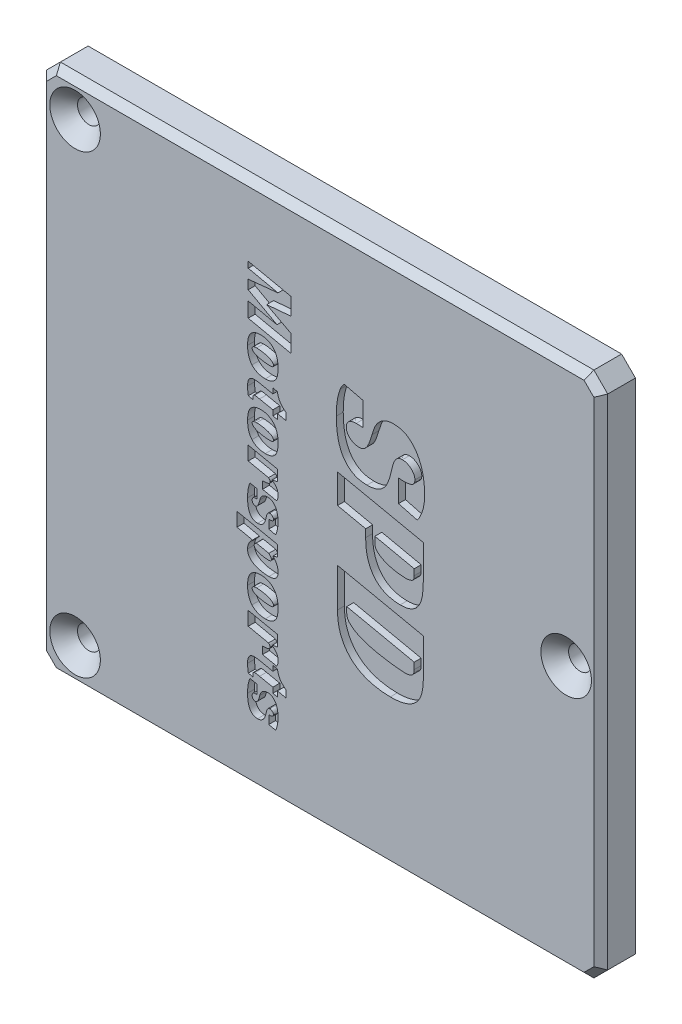
SolidWorks part; units mm, degrees
ref_plane "Front Plane" through (0, 0, 0) normal (0, 0, 1) x (1, 0, 0)
ref_plane "Top Plane" through (0, 0, 0) normal (0, 1, 0) x (1, 0, 0)
ref_plane "Right Plane" through (0, 0, 0) normal (1, 0, 0) x (0, 0, -1)
sketch "Sketch1" plane through (0, 0, 0) normal (0, 0, 1) x (1, 0, 0)
  line L0 (-40, 35) -> (-41, 35) construction
  line L1 (-2, -29) -> (-28, -29) construction
  line L2 (-2, -29) -> (-2, 29) construction
  line L3 (-2, 29) -> (-28, 29) construction
  line L4 (-28, -29) -> (-28, 29) construction
  line L5 (-2, -29) -> (-28, 29) construction
  line L6 (-2, 29) -> (-28, -29) construction
  line L7 (35, -35) -> (-40, -35)
  line L8 (35, -35) -> (35, 35)
  line L9 (35, 35) -> (-40, 35)
  line L10 (-40, -35) -> (-40, 35)
  line L11 (35, -35) -> (-40, 35) construction
  line L12 (35, 35) -> (-40, -35) construction
  line L13 (-40, 35) -> (-40, 36) construction
  line L14 (-41, 35) -> (-5, 35) construction
  line L15 (36, -36) -> (-41, -36)
  line L16 (36, -36) -> (36, 36)
  line L17 (36, 36) -> (-41, 36)
  line L18 (-41, -36) -> (-41, 36)
  line L19 (36, -36) -> (-41, 36) construction
  line L20 (36, 36) -> (-41, -36) construction
  line L21 (-40, 36) -> (-40, 38) construction
  line L22 (0, 0) -> (-15, 0)
  line L23 (38, -38) -> (-43, -38)
  line L24 (38, -38) -> (38, 38)
  line L25 (38, 38) -> (-43, 38)
  line L26 (-43, -38) -> (-43, 38)
  line L27 (38, -38) -> (-43, 38) construction
  line L28 (38, 38) -> (-43, -38) construction
  circle A0 centre (-2, 29) radius 1.25
  circle A1 centre (-28, 29) radius 1.25
  circle A2 centre (-2, -29) radius 1.25
  circle A3 centre (-28, -29) radius 1.25
  point P0 (-15, 0)
  point P10 (-15, 0)
  point P15 (-15, 0)
  point P18 (-15, 0)
  point P24 (-15, 0)
  dimension "D3" = 1
  dimension "D1" = 58
  dimension "D2" = 26
  dimension "D4" = 1
  dimension "D5" = 75
  dimension "D6" = 70
  dimension "D7" = 72
  dimension "D8" = 76
  dimension "D9" = 15
extrude "Boss-Extrude1" add sketch "Sketch1" along normal blind 5
chamfer "Chamfer3" distance 2 angle 45 4 edges at (-43, 38, 2.5) (-43, -38, 2.5) (38, -38, 2.5) (38, 38, 2.5)
sketch "Sketch3" plane through (0, 0, 0) normal (0, 0, -1) x (-1, 0, 0)
  line L0 (-34.92, 32.1764) -> (-34.92, 3.9876)
  line L1 (-33.5482, 34.3518) -> (-34.3518, 33.5482)
  line L2 (-34.92, 1.93) -> (-36, 1.75)
  line L3 (39.77, -26.8512) -> (39.77, 26.8512)
  line L4 (31.7012, 34.92) -> (-32.1764, 34.92)
  line L5 (-34.92, 3.9876) -> (-34.92, 1.93)
  line L6 (-34.3518, -33.5482) -> (-33.5482, -34.3518)
  line L7 (-36, 4.1109) -> (-36, 1.75)
  line L8 (-32.1764, -34.92) -> (31.7012, -34.92)
  line L9 (-34.92, -3.9876) -> (-34.92, -32.1764)
  line L10 (0, 0) -> (-7.0484, 0) construction
  line L11 (-36, -4.1109) -> (-36, -1.75)
  line L12 (-34.92, -3.9876) -> (-34.92, -1.93)
  line L13 (-34.92, -1.93) -> (-36, -1.75)
  line L20 (-34, -36) -> (36.7574, -36)
  line L21 (41, -31.7574) -> (41, 31.7574)
  line L22 (36.7574, 36) -> (-34, 36)
  line L23 (-34, 36) -> (-36, 34)
  line L24 (-36, 34) -> (-36, 1.75)
  line L25 (-36, 1.75) -> (-30, 2.75)
  line L26 (-30, 2.75) -> (-30, -2.75)
  line L27 (-30, -2.75) -> (-36, -1.75)
  line L28 (-36, -1.75) -> (-36, -34)
  line L29 (-36, -34) -> (-34, -36)
  line L30 (-33.1716, -36) -> (32.6816, -36)
  line L31 (41, -27.6816) -> (41, 27.6816)
  line L32 (32.6816, 36) -> (-33.1716, 36)
  line L33 (-34.5858, 35.4142) -> (-35.4142, 34.5858)
  line L34 (-36, 33.1716) -> (-36, 4.1109)
  line L38 (-36, -4.1109) -> (-36, -33.1716)
  line L39 (-35.4142, -34.5858) -> (-34.5858, -35.4142)
  arc A0 (-32.1764, -34.92) -> (-33.5482, -34.3518) centre (-32.1764, -32.98) cw
  arc A1 (33.5976, 32.5708) -> (37.4208, 28.7476) centre (36.7423, 31.8923) ccw
  arc A2 (37.4208, -28.7476) -> (33.5976, -32.5708) centre (36.7423, -31.8923) ccw
  arc A4 (-32.1764, 34.92) -> (-33.5482, 34.3518) centre (-32.1764, 32.98) ccw
  arc A13 (41, -31.7574) -> (36.7574, -36) centre (37.8787, -32.8787) ccw
  arc A14 (36.7574, 36) -> (41, 31.7574) centre (37.8787, 32.8787) ccw
  arc A15 (38.5782, -29.6367) -> (34.6367, -33.5782) centre (37.8787, -32.8787) ccw
  arc A16 (34.6367, 33.5782) -> (38.5782, 29.6367) centre (37.8787, 32.8787) ccw
  arc A17 (32.6816, -36) -> (34.6367, -33.5782) centre (32.6816, -34) ccw
  arc A18 (38.5782, -29.6367) -> (41, -27.6816) centre (39, -27.6816) ccw
  arc A19 (41, 27.6816) -> (38.5782, 29.6367) centre (39, 27.6816) ccw
  arc A20 (34.6367, 33.5782) -> (32.6816, 36) centre (32.6816, 34) ccw
  arc A21 (-36, -33.1716) -> (-35.4142, -34.5858) centre (-34, -33.1716) ccw
  arc A22 (-33.1716, -36) -> (-34.5858, -35.4142) centre (-33.1716, -34) cw
  arc A23 (-33.1716, 36) -> (-34.5858, 35.4142) centre (-33.1716, 34) ccw
  arc A24 (-35.4142, 34.5858) -> (-36, 33.1716) centre (-34, 33.1716) ccw
  arc A25 (39.77, 26.8512) -> (37.4208, 28.7476) centre (37.83, 26.8512) ccw
  arc A26 (-34.92, -32.1764) -> (-34.3518, -33.5482) centre (-32.98, -32.1764) ccw
  arc A28 (-34.3518, 33.5482) -> (-34.92, 32.1764) centre (-32.98, 32.1764) ccw
  arc A30 (33.5976, 32.5708) -> (31.7012, 34.92) centre (31.7012, 32.98) ccw
  arc A31 (37.4208, -28.7476) -> (39.77, -26.8512) centre (37.83, -26.8512) ccw
  arc A33 (31.7012, -34.92) -> (33.5976, -32.5708) centre (31.7012, -32.98) ccw
  dimension "D6" = 2
  dimension "D4" = 0
extrude "Boss-Extrude3" add sketch "Sketch3" along normal blind 2
sketch "Sketch4" plane through (0, 0, 0) normal (0, 0, -1) x (-1, 0, 0)
  line L0 (-30, 2.75) -> (-30, -2.75) construction
  line L1 (-36, 1.75) -> (-36, -1.75) construction
  line L2 (-36, -1.75) -> (-30, -2.75) construction
  line L3 (-30, 0) -> (-36, 0) construction
  circle A0 centre (37.8787, 32.8787) radius 1.65
  circle A1 centre (37.8787, -32.8787) radius 1.65
  circle A2 centre (-33, 0) radius 1.65
  point P2 (37.8787, 32.8787)
  dimension "D2" = 3.3
extrude "Cut-Extrude1" cut sketch "Sketch4" against normal up to surface (5 mm away) up to face at (-2.5, 0, 5)
chamfer "Chamfer4" distance 2 angle 45 3 edges at (-36.2287, -32.8787, 5) (34.65, 0, 5) (-36.2287, 32.8787, 5)
chamfer "Chamfer5" distance 1 angle 45 8 edges at (-42, -37, 5) (-43, 0, 5) (-42, 37, 5) (-2.5, 38, 5) (37, 37, 5) (38, 0, 5) (37, -37, 5) (-2.5, -38, 5)
sketch "Sketch5" plane through (0, 0, 5) normal (0, 0, 1) x (1, 0, 0)
  line L0 (0, 19.0679) -> (0, -20.5631) construction
  line L1 (-12.8935, 27.6478) -> (-12.8935, -32.003) construction
  text T0 "SPD</r>" font "Racing Sans One" height in points 36
  text T1 "Motorsports" font "Racing Sans One" height in points 18
  point P3 (-13.3021, -27.1002)
  point P4 (0, 0)
  point P5 (-13.0978, -32.003)
  point P6 (-12.6892, 25.1964)
  point P7 (0, -20.5631)
  point P11 (-12.8935, 27.6478)
extrude "Cut-Extrude2" cut sketch "Sketch5" against normal blind 1
